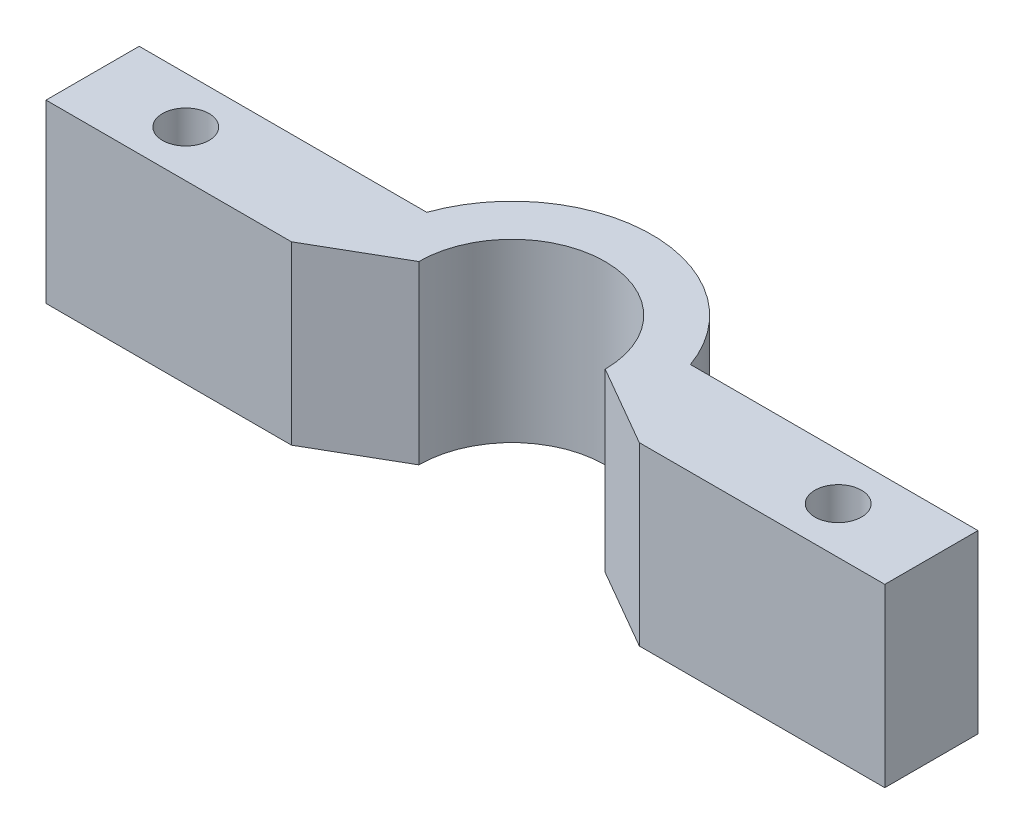
SolidWorks part; units mm, degrees
ref_plane "Front Plane" through (0, 0, 0) normal (0, 0, 1) x (1, 0, 0)
ref_plane "Top Plane" through (0, 0, 0) normal (0, 1, 0) x (1, 0, 0)
ref_plane "Right Plane" through (0, 0, 0) normal (1, 0, 0) x (0, 0, -1)
sketch "Sketch1" plane through (0, 0, 0) normal (0, 1, 0) x (1, 0, 0)
  line L0 (0, 0) -> (4.7625, 0)
  line L1 (-14.2875, -1.5875) -> (14.2875, -1.5875)
  line L2 (-14.2875, -1.5875) -> (-14.2875, 1.5875)
  line L3 (-14.2875, 1.5875) -> (14.2875, 1.5875)
  line L4 (14.2875, -1.5875) -> (14.2875, 1.5875)
  line L5 (-14.2875, -1.5875) -> (14.2875, 1.5875) construction
  line L6 (-14.2875, 1.5875) -> (14.2875, -1.5875) construction
  line L7 (4.7625, 0) -> (-4.7625, 0)
  line L8 (-3.175, 0) -> (-5.9246, -1.5875)
  line L9 (-5.9246, -1.5875) -> (5.9246, -1.5875)
  line L10 (5.9246, -1.5875) -> (3.175, 0)
  circle A0 centre (0, 0) radius 4.7625
  circle A1 centre (0, 0) radius 3.175
  circle A2 centre (-11.1125, 0) radius 0.7937
  circle A3 centre (11.1125, 0) radius 0.7937
  point P0 (0, 0)
  dimension "D3" = 1.5875
  dimension "D4" = 9.525
  dimension "D6" = 1.5875
  dimension "D7" = 3.175
  dimension "D1" = 28.575
  dimension "D2" = 3.175
  dimension "D5" = 3.175
  dimension "D8" = 3.175
extrude "Boss-Extrude1" add sketch "Sketch1" along normal mid plane 6
